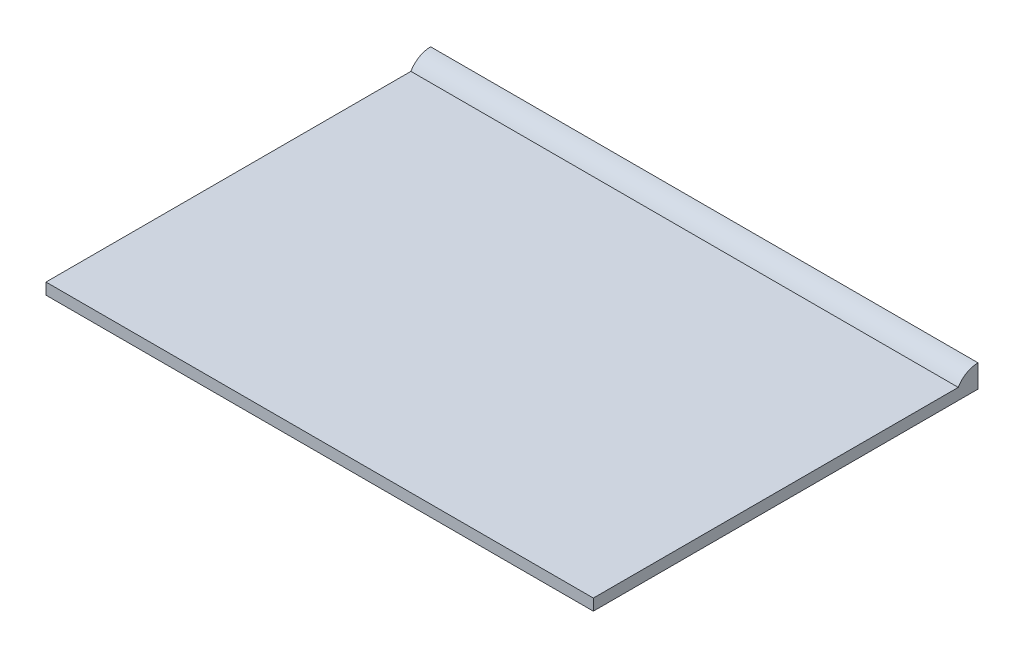
SolidWorks part; units mm, degrees
ref_plane "Front Plane" through (0, 0, 0) normal (0, 0, 1) x (1, 0, 0)
ref_plane "Top Plane" through (0, 0, 0) normal (0, 1, 0) x (1, 0, 0)
ref_plane "Right Plane" through (0, 0, 0) normal (1, 0, 0) x (0, 0, -1)
sketch "Sketch1" plane through (0, 0, 0) normal (0, 1, 0) x (1, 0, 0)
  line L1 (0, 0) -> (19.05, 0)
  line L2 (0, 0) -> (0, 12.7)
  line L3 (0, 12.7) -> (19.05, 12.7)
  line L4 (19.05, 0) -> (19.05, 12.7)
  dimension "D1" = 19.05
  dimension "D2" = 12.7
extrude "Boss-Extrude1" add sketch "Sketch1" along normal blind 0.7937
sketch "Sketch2" plane through (19.05, 0, 0) normal (1, 0, 0) x (0, 0, -1)
  line L0 (0, 0.3969) -> (13.3874, 0.3969) construction
  line L1 (0, 0.7937) -> (0, 0) construction
  circle A0 centre (13.3874, 0.3969) radius 0.7937
  dimension "D1" = 1.5875
extrude "Boss-Extrude2" add sketch "Sketch2" against normal up to surface (19.05 mm away) up to face at (0, 0.3969, -6.35)
sketch "Sketch3" [suppressed] plane through (19.05, 0, 0) normal (1, 0, 0) x (0, 0, -1)
  line L0 (0, 0.3969) -> (13.3874, 0.3969)
  line L1 (0, 0.7937) -> (0, 0) construction
  line L2 (13.3874, 0.3969) -> (13.3874, -0.3969)
  line L4 (14.1812, 0.3969) -> (14.1812, 1.1906)
  line L5 (14.1812, 1.1906) -> (0, 1.1906)
  line L6 (0, 1.1906) -> (0, 0.3969)
  line L7 (13.3874, -0.3969) -> (14.1812, -0.3969)
  line L8 (14.1812, -0.3969) -> (14.1812, 0.3969)
  arc A1 (12.7, 0) -> (12.7, 0.7937) centre (13.3874, 0.3969) ccw construction
extrude "Cut-Extrude1" [suppressed] cut sketch "Sketch3" against normal through all
sketch "Sketch4" plane through (19.05, 0, 0) normal (1, 0, 0) x (0, 0, -1)
  line L0 (0, 0.3969) -> (13.3874, 0.3969)
  line L1 (0, 0.7937) -> (0, 0) construction
  line L2 (13.3874, 0.3969) -> (13.3874, 1.1906)
  line L3 (0, 0.3969) -> (0, -0.3969)
  line L4 (0, -0.3969) -> (14.1812, -0.3969)
  line L5 (14.1812, -0.3969) -> (14.1812, 1.1906)
  line L6 (14.1812, 1.1906) -> (13.3874, 1.1906)
  arc A0 (12.7, 0) -> (12.7, 0.7937) centre (13.3874, 0.3969) ccw construction
extrude "Cut-Extrude2" cut sketch "Sketch4" against normal through all
